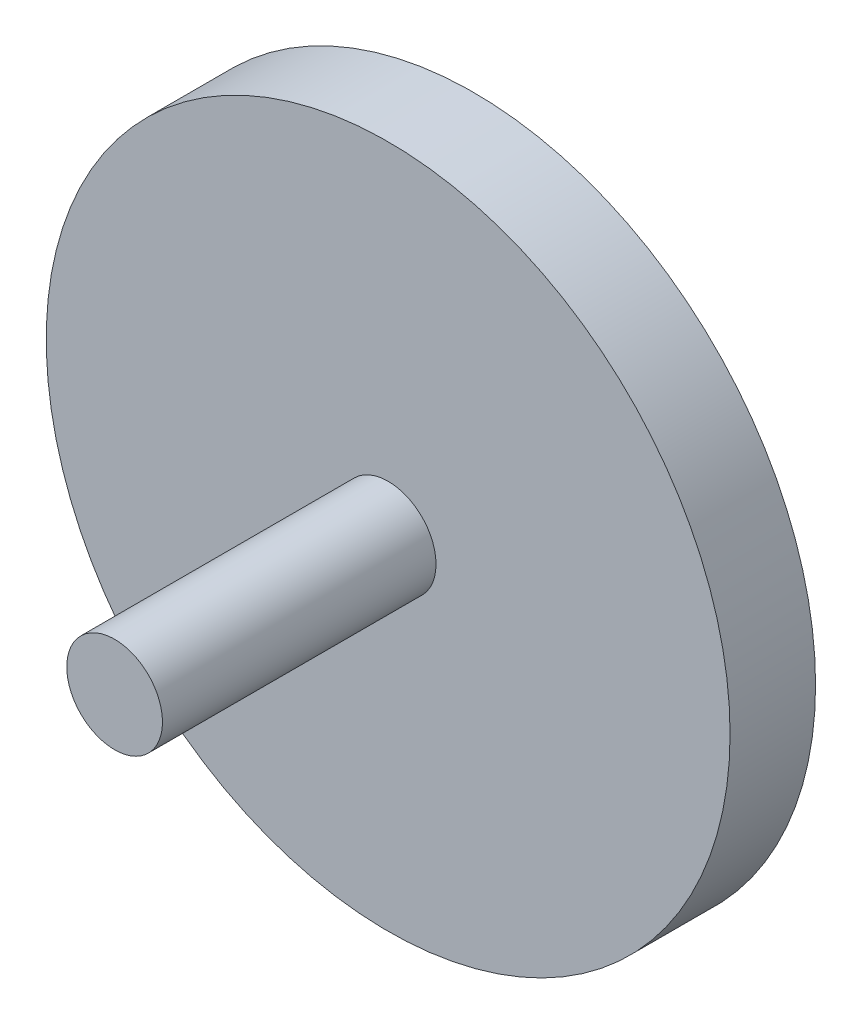
SolidWorks part; units mm, degrees
ref_plane "Front Plane" through (0, 0, 0) normal (0, 0, 1) x (1, 0, 0)
ref_plane "Top Plane" through (0, 0, 0) normal (0, 1, 0) x (1, 0, 0)
ref_plane "Right Plane" through (0, 0, 0) normal (1, 0, 0) x (0, 0, -1)
sketch "Sketch1" plane through (0, 0, 0) normal (0, 0, 1) x (1, 0, 0)
  circle A0 centre (0, 0) radius 100
  dimension "D1" = 200
extrude "Boss-Extrude1" add sketch "Sketch1" along normal blind 25
sketch "Sketch2" plane through (0, 0, 25) normal (0, 0, 1) x (1, 0, 0)
  circle A0 centre (0, 0) radius 14
  dimension "D1" = 28
extrude "Boss-Extrude2" add sketch "Sketch2" along normal blind 80 contours A0
sketch "Sketch3" plane through (0, 0, 0) normal (0, 0, -1) x (-1, 0, 0)
  circle A0 centre (0, 50) radius 10
  dimension "D1" = 20
  dimension "D2" = 50
extrude "Cut-Extrude1" cut sketch "Sketch3" against normal blind 4 contours A0
